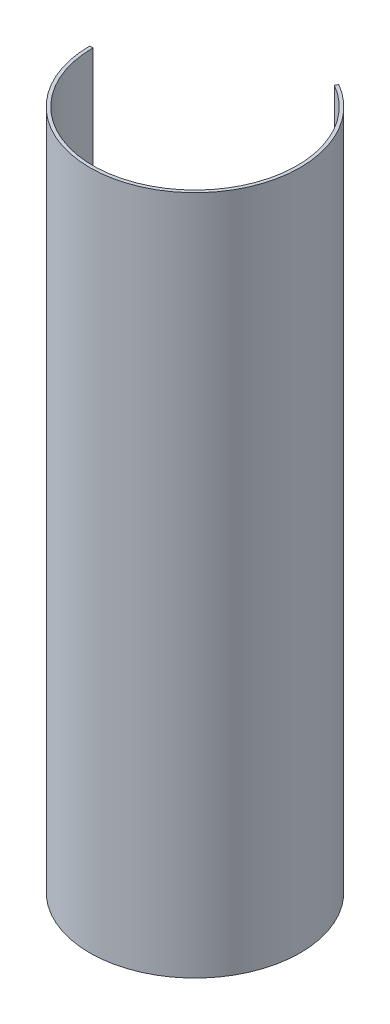
SolidWorks part; units mm, degrees
material "Acrylic (Medium-high impact)"
ref_plane "Front Plane" through (0, 0, 0) normal (0, 0, 1) x (1, 0, 0)
ref_plane "Top Plane" through (0, 0, 0) normal (0, 1, 0) x (1, 0, 0)
ref_plane "Right Plane" through (0, 0, 0) normal (1, 0, 0) x (0, 0, -1)
sketch "Sketch1" plane through (0, 0, 0) normal (0, 1, 0) x (1, 0, 0)
  circle A0 centre (0, 0) radius 40.005
  circle A1 centre (0, 0) radius 41.275
  dimension "D1" = 1.27
  dimension "D2" = 80.01
extrude "Boss-Extrude1" add sketch "Sketch1" along normal blind 266.7
sketch "Sketch3" plane through (0, 0, 0) normal (0, 1, 0) x (1, 0, 0)
  line L0 (0, 0) -> (-129.0528, 0)
  line L1 (-129.0528, 0) -> (91.7275, 158.8766)
  line L2 (91.7275, 158.8766) -> (0, 0)
  dimension "D1" = 120
extrude "Cut-Extrude3" cut sketch "Sketch3" along normal through all
